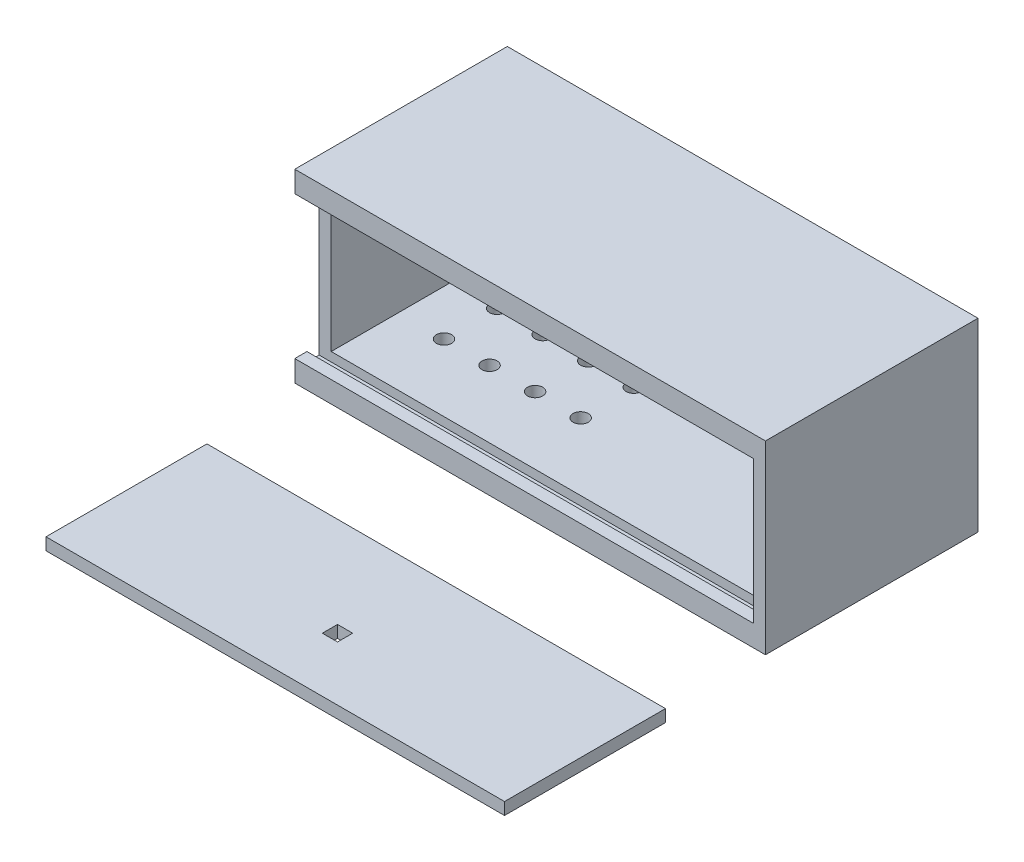
SolidWorks part; units mm, degrees
ref_plane "Piano frontale" through (0, 0, 0) normal (0, 0, 1) x (1, 0, 0)
ref_plane "Piano superiore" through (0, 0, 0) normal (0, 1, 0) x (1, 0, 0)
ref_plane "Piano destro" through (0, 0, 0) normal (1, 0, 0) x (0, 0, -1)
sketch "Schizzo1" plane through (0, 0, 0) normal (0, 1, 0) x (1, 0, 0)
  line L0 (-119.5492, 58) -> (27.4508, 58)
  line L1 (-123.5492, 62) -> (31.4508, 62)
  line L2 (-123.5492, 62) -> (-123.5492, -8)
  line L3 (-123.5492, -8) -> (31.4508, -8)
  line L4 (31.4508, 62) -> (31.4508, -8)
  line L5 (-123.5492, 62) -> (31.4508, -8) construction
  line L6 (-123.5492, -8) -> (31.4508, 62) construction
  line L7 (27.4508, 58) -> (27.4508, 0)
  line L8 (27.4508, 0) -> (-119.5492, 0)
  line L9 (-119.5492, 0) -> (-119.5492, 58)
  line L10 (27.4508, 0) -> (27.4508, -8)
  line L11 (-123.5492, -4) -> (27.4508, -4)
  line L12 (-119.5492, 0) -> (-123.5492, 0)
  point P0 (-46.0492, 27)
  dimension "D1" = 155
  dimension "D2" = 70
  dimension "D3" = 4
  dimension "D4" = 4
  dimension "D5" = 4
  dimension "D6" = 8
  dimension "D7" = 4
extrude "Estrusione-Estrusione7" add sketch "Schizzo1" along normal blind 4 contours L12 L9 L0 L7 L10 L3 L4 L1 L2 | L9 L8 L7 L0 | L8 L12 L2 L11 L10 | L11 L2 L3 L10
ref_plane "Piano1" through (0, 4, 0) normal (0, 1, 0) x (1, 0, 0)
sketch "Schizzo8" plane through (0, 4, 0) normal (0, 1, 0) x (1, 0, 0)
  line L0 (-119.5492, 58) -> (27.4508, 58)
  line L1 (27.4508, 58) -> (27.4508, 0)
  line L2 (27.4508, 0) -> (-119.5492, 0)
  line L3 (-119.5492, 0) -> (-119.5492, 58)
  line L4 (27.4508, 0) -> (27.4508, -8)
  line L5 (-123.5492, -8) -> (31.4508, -8) construction
  line L6 (27.4508, -4) -> (-123.5492, -4)
  line L7 (-123.5492, 62) -> (-123.5492, -8) construction
  line L8 (-119.5492, 0) -> (-123.5492, 0)
  line L9 (-123.5492, 62) -> (31.4508, 62) construction
  line L10 (31.4508, 62) -> (31.4508, -8) construction
  line L11 (31.4508, 62) -> (31.4508, -8)
  line L12 (-123.5492, -8) -> (31.4508, -8)
  line L13 (-123.5492, 62) -> (-123.5492, -8)
  line L14 (-123.5492, 62) -> (31.4508, 62)
  dimension "D1" = 4
  dimension "D2" = 4
  dimension "D3" = 4
  dimension "D4" = 4
  dimension "D5" = 4
extrude "Estrusione-Estrusione9" add sketch "Schizzo8" along normal blind 3 contours L14 L13 L8 L3 L0 L1 L4 L12 L11 | L3 L2 L1 L0 | L6 L13 L12 L4
ref_plane "Piano2" through (-123.5492, 0, 0) normal (-1, 0, 0) x (0, 0, 1)
ref_plane "Piano3" through (0, 7, 0) normal (0, 1, 0) x (1, 0, 0)
sketch "Schizzo15" plane through (0, 7, 0) normal (0, 1, 0) x (1, 0, 0)
  line L0 (31.4508, 62) -> (31.4508, -8) construction
  line L1 (27.4508, 0) -> (27.4508, -4) construction
  line L2 (-123.5492, -8) -> (31.4508, -8) construction
  line L3 (-123.5492, -4) -> (-123.5492, -8) construction
  line L4 (-123.5492, 0) -> (-123.5492, -4) construction
  line L5 (27.4508, -4) -> (-123.5492, -4) construction
  line L6 (27.4508, 0) -> (-123.5492, 0) construction
  line L7 (-123.5492, 62) -> (-123.5492, 0) construction
  line L8 (-123.5492, 62) -> (31.4508, 62) construction
  line L9 (31.4508, 62) -> (31.4508, -8)
  line L10 (27.4508, 0) -> (27.4508, -4)
  line L11 (-123.5492, -8) -> (31.4508, -8)
  line L12 (-123.5492, -4) -> (-123.5492, -8)
  line L13 (-123.5492, 0) -> (-123.5492, -4)
  line L14 (27.4508, -4) -> (-123.5492, -4)
  line L15 (27.4508, 0) -> (-123.5492, 0)
  line L16 (-123.5492, 62) -> (-123.5492, 0)
  line L17 (-123.5492, 62) -> (31.4508, 62)
  line L18 (-119.5492, 0) -> (-119.5492, 58)
  line L19 (-119.5492, 58) -> (27.4508, 58)
  line L20 (27.4508, 58) -> (27.4508, 0)
  line L21 (27.4508, -4) -> (27.4508, -8)
  dimension "D1" = 4
  dimension "D2" = 4
extrude "Estrusione-Estrusione10" add sketch "Schizzo15" along normal blind 54 contours L10 L21 L11 L9 L17 L16 L15 L18 L19 L20
ref_plane "Piano4" through (0, 61, 0) normal (0, 1, 0) x (1, 0, 0)
sketch "Schizzo18" plane through (0, 61, 0) normal (0, 1, 0) x (1, 0, 0)
  line L0 (-119.5492, 58) -> (27.4508, 58) construction
  line L1 (-119.5492, 0) -> (27.4508, 0)
  line L2 (-119.5492, 0) -> (-119.5492, 58)
  line L3 (-119.5492, 58) -> (27.4508, 58)
  line L4 (27.4508, 0) -> (27.4508, 58)
  line L5 (-119.5492, 0) -> (27.4508, 58) construction
  line L6 (-119.5492, 58) -> (27.4508, 0) construction
  line L7 (-119.5492, 0) -> (-119.5492, 58) construction
  point P0 (-46.0492, 29)
extrude "Estrusione-Estrusione11" add sketch "Schizzo18" against normal blind 7
sketch "Schizzo19" plane through (0, 61, 0) normal (0, 1, 0) x (1, 0, 0)
  line L0 (27.4508, 0) -> (-123.5492, 0)
  line L1 (-123.5492, 0) -> (-123.5492, -4)
  line L2 (-123.5492, -4) -> (27.4508, -4)
  line L3 (27.4508, 0) -> (27.4508, -8) construction
  line L4 (27.4508, -4) -> (27.4508, 0)
extrude "Estrusione-Estrusione12" add sketch "Schizzo19" against normal blind 4
sketch "Schizzo20" plane through (0, 61, 0) normal (0, 1, 0) x (1, 0, 0)
  line L0 (-123.5492, -4) -> (-123.5492, -8)
  line L1 (-123.5492, -4) -> (-123.5492, -8) construction
  line L2 (-123.5492, -8) -> (27.4508, -8)
  line L3 (27.4508, -4) -> (27.4508, -8) construction
  line L4 (27.4508, -8) -> (27.4508, -4)
  line L5 (27.4508, -4) -> (-123.5492, -4)
extrude "Estrusione-Estrusione13" add sketch "Schizzo20" against normal blind 7 contours L5 L0 L2 L4
ref_plane "Piano5" through (-123.5492, 0, 0) normal (-1, 0, 0) x (0, 0, 1)
sketch "Schizzo21" plane through (-123.5492, 0, 0) normal (-1, 0, 0) x (0, 0, 1)
  line L0 (-62, 0) -> (8, 0) construction
  line L1 (-43, 40) -> (-29, 40)
  line L2 (-43, 40) -> (-43, 22)
  line L3 (-43, 22) -> (-29, 22)
  line L4 (-29, 40) -> (-29, 22)
  line L5 (-43, 40) -> (-29, 22) construction
  line L6 (-43, 22) -> (-29, 40) construction
  line L7 (-62, 61) -> (-62, 0) construction
  point P0 (-36, 31)
  dimension "D1" = 22
  dimension "D2" = 18
  dimension "D3" = 14
  dimension "D4" = 19
extrude "Taglio-Estrusione1" cut sketch "Schizzo21" against normal blind 7
ref_plane "Piano6" through (0, 0, -62) normal (0, 0, -1) x (-1, 0, 0)
sketch "Schizzo22" plane through (0, 0, -62) normal (0, 0, -1) x (-1, 0, 0)
  line L0 (38.5, 61) -> (-38.5, 61) construction
  line L1 (-20.4508, 46) -> (59.5492, 46)
  line L2 (-20.4508, 46) -> (-20.4508, 14)
  line L3 (-20.4508, 14) -> (59.5492, 14)
  line L4 (59.5492, 46) -> (59.5492, 14)
  line L5 (-20.4508, 46) -> (59.5492, 14) construction
  line L6 (-20.4508, 14) -> (59.5492, 46) construction
  line L7 (-31.4508, 61) -> (-31.4508, 0) construction
  point P0 (19.5492, 30)
  dimension "D1" = 15
  dimension "D2" = 80
  dimension "D3" = 11
  dimension "D4" = 32
extrude "Taglio-Estrusione2" cut sketch "Schizzo22" against normal blind 7
ref_plane "Piano7" through (0, 0, 0) normal (0, -1, 0) x (-1, 0, 0)
sketch "Schizzo23" plane through (0, 0, 0) normal (0, -1, 0) x (-1, 0, 0)
  line L0 (123.5492, 62) -> (123.5492, -8) construction
  line L1 (123.5492, 62) -> (-31.4508, 62) construction
  circle A0 centre (104.5492, 39.65) radius 2.5
  circle A1 centre (104.5492, 22.15) radius 2.5
  circle A2 centre (89.5492, 39.65) radius 2.5
  circle A3 centre (89.5492, 22.15) radius 2.5
  circle A4 centre (74.5492, 39.65) radius 2.5
  circle A5 centre (74.5492, 22.15) radius 2.5
  circle A6 centre (59.5492, 39.65) radius 2.5
  circle A7 centre (59.5492, 22.15) radius 2.5
  point P16 (0, 0)
  point P17 (0, 0)
  point P22 (0, 0)
  point P23 (0, 0)
  dimension "D1" = 5
  dimension "D2" = 5
  dimension "D3" = 5
  dimension "D4" = 5
  dimension "D5" = 5
  dimension "D6" = 5
  dimension "D8" = 15
  dimension "D9" = 15
  dimension "D10" = 17.5
  dimension "D11" = 22.35
  dimension "D12" = 5
  dimension "D13" = 5
  dimension "D7" = 19
  dimension "D14" = 15
extrude "Taglio-Estrusione3" cut sketch "Schizzo23" against normal blind 10
sketch "Schizzo29" plane through (0, 0, 0) normal (0, 1, 0) x (1, 0, 0)
  line L1 (-116.6756, -96.7958) -> (34.3244, -96.7958)
  line L2 (-116.6756, -96.7958) -> (-116.6756, -43.7958)
  line L3 (-116.6756, -43.7958) -> (34.3244, -43.7958)
  line L4 (34.3244, -96.7958) -> (34.3244, -43.7958)
  line L5 (-116.6756, -96.7958) -> (34.3244, -43.7958) construction
  line L6 (-116.6756, -43.7958) -> (34.3244, -96.7958) construction
  line L7 (27.4508, -4) -> (27.4508, 0) construction
  line L9 (27.4508, -4) -> (27.4508, 0)
  line L11 (-43.6756, -73.7958) -> (-38.6756, -73.7958)
  line L12 (-43.6756, -73.7958) -> (-43.6756, -78.7958)
  line L13 (-43.6756, -78.7958) -> (-38.6756, -78.7958)
  line L14 (-38.6756, -73.7958) -> (-38.6756, -78.7958)
  line L15 (-43.6756, -73.7958) -> (-38.6756, -78.7958) construction
  line L16 (-43.6756, -78.7958) -> (-38.6756, -73.7958) construction
  point P0 (-41.1756, -70.2958)
  point P9 (-41.1756, -76.2958)
  dimension "D1" = 151
  dimension "D2" = 53
  dimension "D3" = 73
  dimension "D4" = 5
  dimension "D5" = 5
  dimension "D6" = 18
extrude "Estrusione-Estrusione14" add sketch "Schizzo29" along normal blind 4 separate body contours L1 L4 L3 L2 L11 L14 L13 L12
